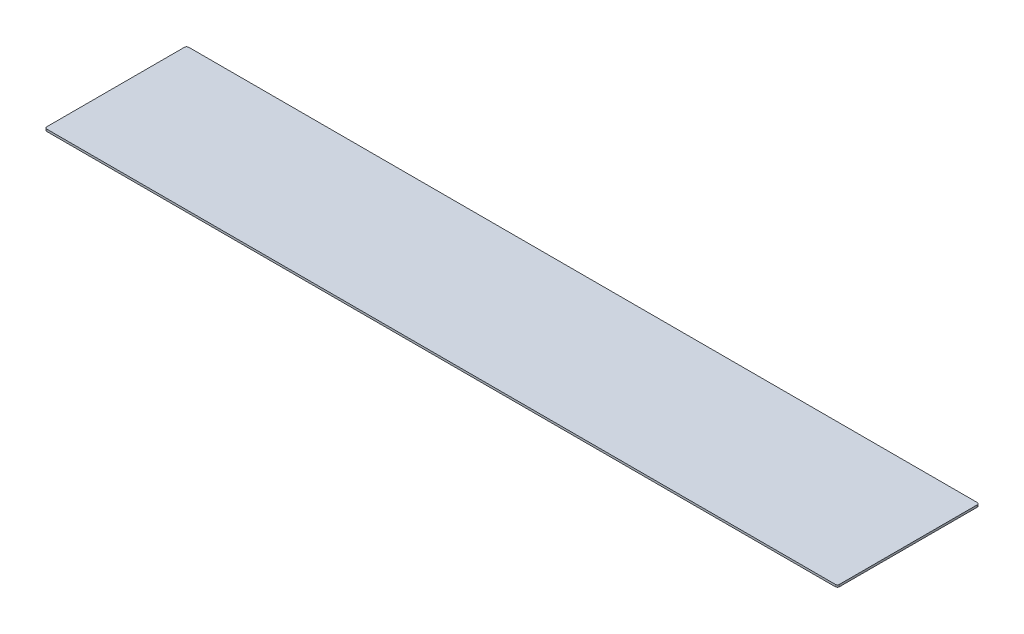
SolidWorks part; units mm, degrees
material "PC High Viscosity"
ref_plane "Front Plane" through (0, 0, 0) normal (0, 0, 1) x (1, 0, 0)
ref_plane "Top Plane" through (0, 0, 0) normal (0, 1, 0) x (1, 0, 0)
ref_plane "Right Plane" through (0, 0, 0) normal (1, 0, 0) x (0, 0, -1)
sketch "Sketch1" plane through (0, 0, 0) normal (0, 1, 0) x (1, 0, 0)
  line L1 (-591.185, -106.3625) -> (591.185, -106.3625)
  line L2 (-594.36, -103.1875) -> (-594.36, 103.1875)
  line L3 (-591.185, 106.3625) -> (591.185, 106.3625)
  line L4 (594.36, -103.1875) -> (594.36, 103.1875)
  line L5 (-594.36, -106.3625) -> (594.36, 106.3625) construction
  line L6 (-594.36, 106.3625) -> (594.36, -106.3625) construction
  arc A0 (591.185, 106.3625) -> (594.36, 103.1875) centre (591.185, 103.1875) cw
  arc A1 (591.185, -106.3625) -> (594.36, -103.1875) centre (591.185, -103.1875) ccw
  arc A2 (-591.185, -106.3625) -> (-594.36, -103.1875) centre (-591.185, -103.1875) cw
  arc A3 (-594.36, 103.1875) -> (-591.185, 106.3625) centre (-591.185, 103.1875) cw
  point P0 (0, 0)
  dimension "D3" = 3.175
  dimension "D1" = 1188.72
  dimension "D2" = 212.725
extrude "Boss-Extrude1" add sketch "Sketch1" along normal blind 3.175
sketch "Sketch2" plane through (0, 3.175, 0) normal (0, 1, 0) x (1, 0, 0)
  line L2 (-406.4, -96.8375) -> (406.4, -96.8375) construction
  line L3 (-591.185, -106.3625) -> (591.185, -106.3625) construction
  point P2 (0, -96.8375)
  point P12 (0, -96.8375)
  dimension "D1" = 812.8
  dimension "D3" = 9.525
hole_wizard "1/4 (0.25) Diameter Hole1" positions "Sketch3" profile "Sketch4" hole size "1/4" standard "ANSI Inch"
sketch "Sketch3" plane through (0, 3.175, 0) normal (0, 1, 0) x (1, 0, 0)
  point P9 (0, -96.8375)
  point P28 (-406.4, -96.8375)
  point P31 (406.4, -96.8375)
sketch "Sketch4" plane through (0, 3.175, 96.8375) normal (1, 0, 0) x (0, 0, 1)
  line L0 (0, 0) -> (0, 3.175)
  line L1 (0, 3.175) -> (3.175, 3.175)
  line L2 (3.175, 3.175) -> (3.175, 0)
  line L5 (3.175, 0) -> (0, 0)
  line L11 (0, -6.35) -> (0, 107.95) construction
  dimension "Thru Hole Dia." = 6.35
  dimension "Thru Hole Depth" = 3.175
sketch "Sketch5" plane through (0, 3.175, 0) normal (0, 1, 0) x (1, 0, 0)
  line L0 (591.185, 106.3625) -> (-591.185, 106.3625) construction
  line L1 (584.2, 36.9087) -> (546.1, 36.9087) construction
  line L2 (584.2, 36.9087) -> (584.2, 87.7087) construction
  line L3 (584.2, 87.7087) -> (546.1, 87.7087) construction
  line L4 (546.1, 36.9087) -> (546.1, 87.7087) construction
  line L5 (584.2, 36.9087) -> (546.1, 87.7087) construction
  line L6 (584.2, 87.7087) -> (546.1, 36.9087) construction
  line L7 (-546.1, 36.9087) -> (-584.2, 36.9087) construction
  line L8 (-546.1, 36.9087) -> (-546.1, 87.7087) construction
  line L9 (-546.1, 87.7087) -> (-584.2, 87.7087) construction
  line L10 (-584.2, 36.9087) -> (-584.2, 87.7087) construction
  line L11 (-546.1, 36.9087) -> (-584.2, 87.7087) construction
  line L12 (-546.1, 87.7087) -> (-584.2, 36.9087) construction
  line L13 (594.36, -103.1875) -> (594.36, 103.1875) construction
  line L14 (-594.36, 103.1875) -> (-594.36, -103.1875) construction
  point P4 (565.15, 62.3087)
  point P9 (-565.15, 62.3087)
  dimension "D1" = 38.1
  dimension "D2" = 50.8
  dimension "D3" = 18.6538
  dimension "D4" = 10.16
  dimension "D5" = 10.16
hole_wizard "17/64 (0.26563) Diameter Hole2" positions "Sketch6" profile "Sketch7" hole size "17/64" standard "ANSI Inch"
sketch "Sketch6" plane through (0, 3.175, 0) normal (0, 1, 0) x (1, 0, 0)
  point P0 (-546.1, 36.9087)
  point P3 (-546.1, 87.7087)
  point P6 (-584.2, 87.7087)
  point P9 (-584.2, 36.9087)
  point P12 (584.2, 36.9087)
  point P15 (546.1, 36.9087)
  point P18 (546.1, 87.7087)
  point P21 (584.2, 87.7087)
sketch "Sketch7" plane through (-546.1, 3.175, -36.9087) normal (1, 0, 0) x (0, 0, 1)
  line L0 (0, 0) -> (0, 3.175)
  line L1 (0, 3.175) -> (3.3735, 3.175)
  line L2 (3.3735, 3.175) -> (3.3735, 0)
  line L5 (3.3735, 0) -> (0, 0)
  line L11 (0, -6.35) -> (0, 107.95) construction
  dimension "Thru Hole Dia." = 6.747
  dimension "Thru Hole Depth" = 3.175
